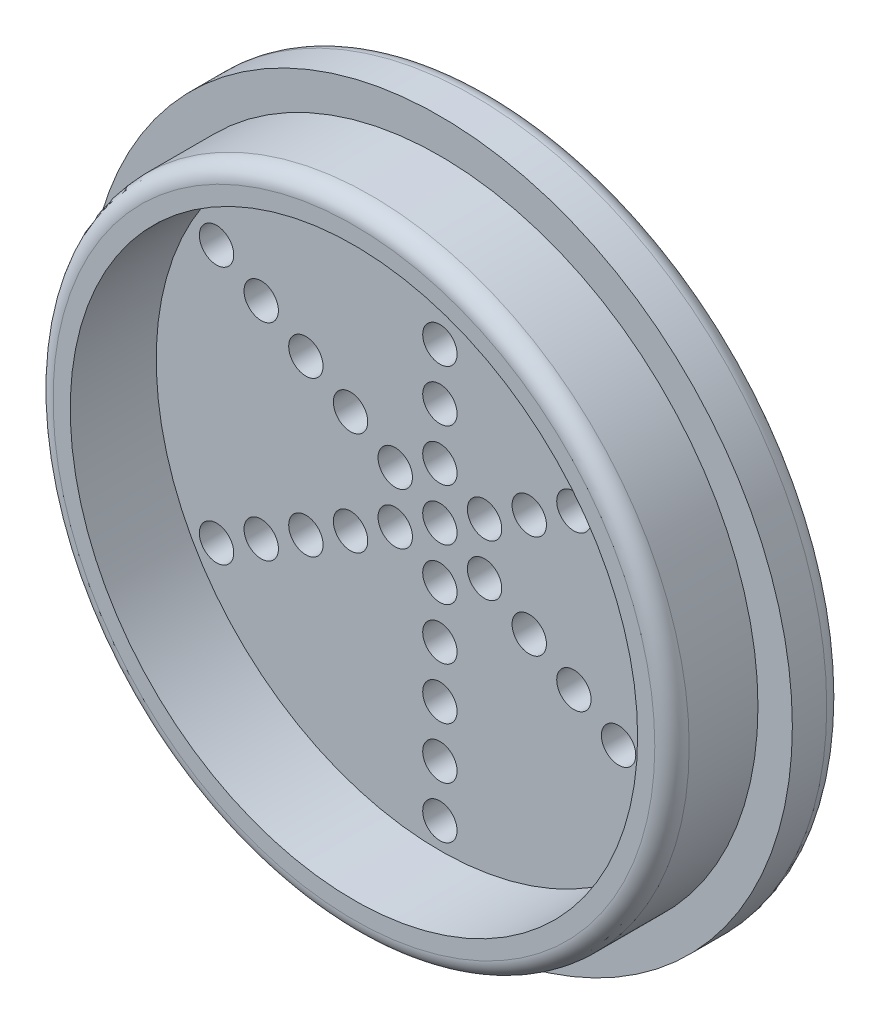
SolidWorks part; units mm, degrees
ref_plane "Front Plane" through (0, 0, 0) normal (0, 0, 1) x (1, 0, 0)
ref_plane "Top Plane" through (0, 0, 0) normal (0, 1, 0) x (1, 0, 0)
ref_plane "Right Plane" through (0, 0, 0) normal (1, 0, 0) x (0, 0, -1)
sketch "Sketch2" plane through (0, 0, 0) normal (0, 0, 1) x (1, 0, 0)
  circle A0 centre (0, 0) radius 20.5
  dimension "D1" = 41
extrude "Boss-Extrude1" add sketch "Sketch2" along normal blind 3
sketch "Sketch3" plane through (0, 0, 3) normal (0, 0, 1) x (1, 0, 0)
  circle A0 centre (0, 0) radius 18.5
  dimension "D1" = 37
extrude "Boss-Extrude2" add sketch "Sketch3" along normal blind 5
sketch "Sketch4" plane through (0, 0, 8) normal (0, 0, 1) x (1, 0, 0)
  circle A0 centre (0, 0) radius 16.5
  circle A1 centre (0, 0) radius 18.5 construction
  dimension "D1" = 2
extrude "Cut-Extrude1" cut sketch "Sketch4" against normal blind 5
fillet "Fillet1" radius 1 1 edges at (18.5, 0, 8)
fillet "Fillet2" radius 1 1 edges at (20.5, 0, 0)
sketch "Sketch9" plane through (0, 0, 0) normal (0, 0, -1) x (-1, 0, 0)
  circle A0 centre (0, 0) radius 1
  dimension "D1" = 2
extrude "Cut-Extrude2" cut sketch "Sketch9" against normal up to surface (3 mm away) up to face at (16.5, 0, 3)
hole_wizard "Ø2.0mm Dowel Hole4" positions "Sketch13" profile "Sketch12" hole size "Ø2.0" standard "ANSI Metric"
sketch "Sketch13" plane through (0, 0, 0) normal (0, 0, -1) x (-1, 0, 0)
  point P0 (0, 3)
  point P4 (0, 6)
  point P6 (0, 9)
  point P8 (0, 12)
  point P10 (0, 15)
  dimension "D1" = 3
  dimension "D2" = 3
  dimension "D3" = 3
  dimension "D4" = 3
  dimension "D5" = 3
sketch "Sketch12" plane through (0, 3, 0) normal (1, 0, 0) x (0, 1, 0)
  line L0 (0, 0) -> (0, 100.6009)
  line L1 (0, 100.6009) -> (1, 100)
  line L2 (1, 100) -> (1, 0)
  line L5 (1, 0) -> (0, 0)
  line L10 (0, 100.6009) -> (-1, 100) construction
  line L11 (0, -6.35) -> (0, 107.95) construction
  dimension "Hole Dia." = 2
  dimension "Hole Depth" = 100
  dimension "Drill Angle" = 118
pattern_circular "CirPattern1" count 6 over 360 about axis through (0, 0, 0) along (0, 0, 1) of "Ø2.0mm Dowel Hole4"
